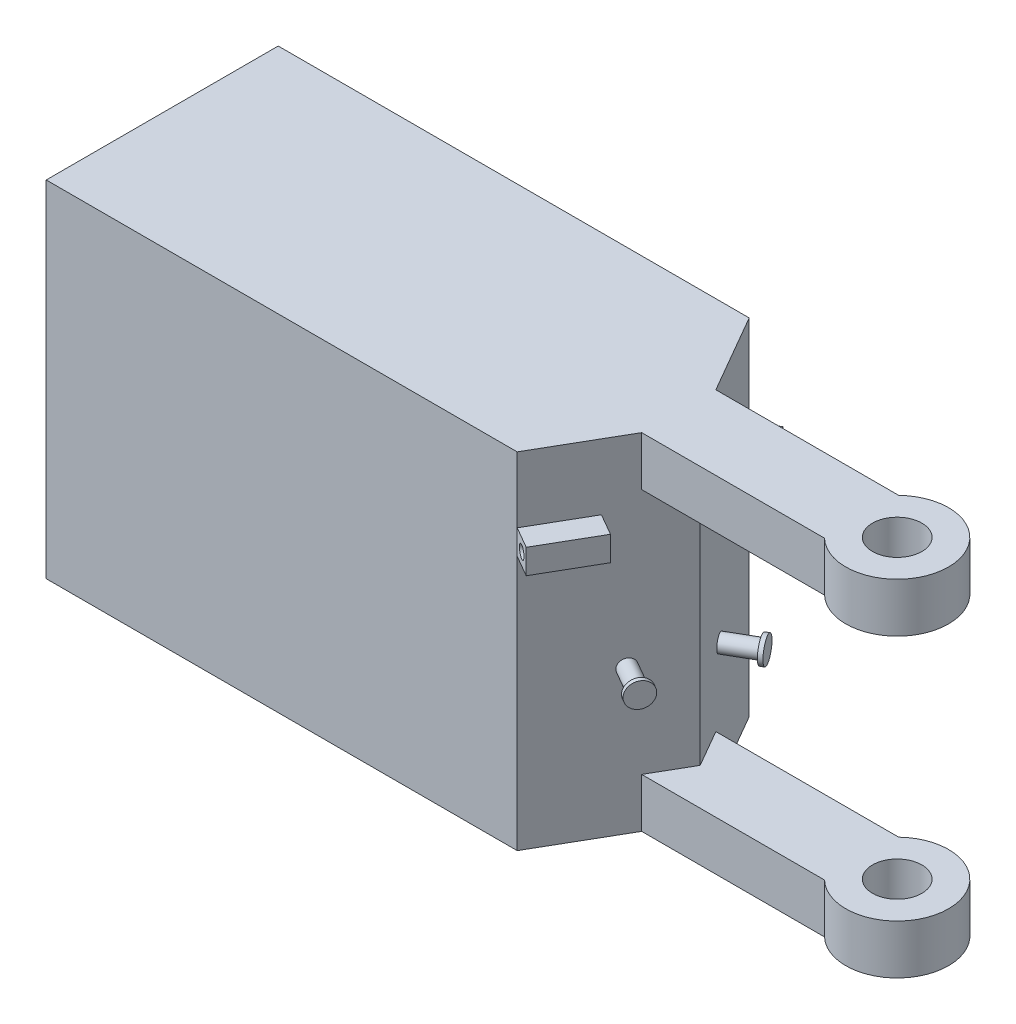
SolidWorks part; units mm, degrees
ref_plane "Front Plane" through (0, 0, 0) normal (0, 0, 1) x (1, 0, 0)
ref_plane "Top Plane" through (0, 0, 0) normal (0, 1, 0) x (1, 0, 0)
ref_plane "Right Plane" through (0, 0, 0) normal (1, 0, 0) x (0, 0, -1)
sketch "Sketch4" plane through (0, 0, 0) normal (0, 1, 0) x (1, 0, 0)
  line L0 (0, 0) -> (220.8953, 0) construction
  line L1 (0, -28.2146) -> (0, 28.2146)
  line L2 (0, 28.2146) -> (114.5561, 28.2146)
  line L3 (114.5561, 28.2146) -> (125.6373, 9.0214)
  line L4 (125.6373, 9.0214) -> (170.1134, 9.0214)
  line L6 (125.6373, -9.0214) -> (170.1134, -9.0214)
  line L7 (114.5561, -28.2146) -> (125.6373, -9.0214)
  line L8 (0, -28.2146) -> (114.5561, -28.2146)
  line L9 (125.6373, 9.0214) -> (130.8458, 0) construction
  circle A0 centre (178.7659, 0) radius 12.5
  circle A2 centre (178.7659, 0) radius 6
  point P9 (176.8194, 0)
  dimension "D3" = 25
  dimension "D4" = 12
  dimension "D1" = 18.0428
  dimension "D2" = 47.9201
  dimension "D5" = 120
  dimension "D6" = 120
extrude "Boss-Extrude2" add sketch "Sketch4" along normal blind 12
sketch "Sketch6" plane through (0, 12, 0) normal (0, 1, 0) x (1, 0, 0)
  line L0 (0, 0) -> (0, 28.2146)
  line L1 (0, -28.2146) -> (0, 28.2146) construction
  line L2 (0, 28.2146) -> (114.5561, 28.2146)
  line L3 (114.5561, 28.2146) -> (125.6373, 9.0214)
  line L4 (125.6373, 9.0214) -> (130.8458, 0)
  line L5 (130.8458, 0) -> (114.5561, -28.2146)
  line L6 (114.5561, -28.2146) -> (0, -28.2146)
  line L7 (0, -28.2146) -> (0, 0)
  line L9 (125.6373, -9.0214) -> (170.1134, -9.0214) construction
  dimension "D1" = 120
extrude "Boss-Extrude3" add sketch "Sketch6" along normal blind 30
mirror "Mirror5" about plane through (0, 42, 0) normal (0, -1, 0) of bodies 103
sketch "Sketch7" plane through (98.1343, 0, 56.6579) normal (0.866, 0, 0.5) x (0.5, 0, -0.866)
  line L6 (52.4079, 42) -> (52.4079, 0) construction
  line L12 (32.8435, 0) -> (55.0059, 0) construction
  line L13 (52.4079, 42) -> (52.4079, 21) construction
sketch "Sketch10" plane through (98.1343, 0, 56.6579) normal (0.866, 0, 0.5) x (0.5, 0, -0.866)
  line L1 (52.4079, 42) -> (52.4079, 0) construction
  line L2 (52.4079, 35) -> (52.4079, 29) construction
sketch "Sketch11" plane through (98.1343, 0, -56.6579) normal (0.866, 0, -0.5) x (-0.5, 0, -0.866)
  line L5 (-52.4079, 21) -> (-52.4079, 29) construction
sketch "Sketch16" plane through (98.1343, 0, -56.6579) normal (0.866, 0, -0.5) x (-0.5, 0, -0.866)
  line L0 (-52.4079, 21) -> (-52.4079, 29) construction
  circle A0 centre (-52.4079, 29) radius 2
extrude "Boss-Extrude9" add sketch "Sketch16" along normal blind 8.5
sketch "Sketch17" plane through (98.1343, 0, 56.6579) normal (0.866, 0, 0.5) x (0.5, 0, -0.866)
  line L0 (52.4079, 0) -> (52.4079, 35) construction
  circle A0 centre (52.4079, 35) radius 2
extrude "Boss-Extrude10" add sketch "Sketch17" along normal blind 8.5
sketch "Sketch9" plane through (98.1343, 0, -56.6579) normal (0.866, 0, -0.5) x (-0.5, 0, -0.866)
sketch "Sketch18" plane through (98.1343, 0, -56.6579) normal (0.866, 0, -0.5) x (-0.5, 0, -0.866)
  line L0 (-32.8435, 84) -> (-32.8435, 59) construction
  line L1 (-32.8435, 84) -> (-32.8435, 0) construction
  line L2 (-32.8435, 59) -> (-32.8435, 56.1904)
  line L3 (-32.8435, 56.1904) -> (-45.94, 56.1904)
  line L4 (-45.94, 56.1904) -> (-45.94, 62.1904)
  line L5 (-45.94, 62.1904) -> (-32.8435, 62.1904)
  line L6 (-32.8435, 62.1904) -> (-32.8435, 59)
  line L7 (-32.8435, 84) -> (-55.0059, 84) construction
  dimension "D1" = 25
extrude "Boss-Extrude11" add sketch "Sketch18" along normal blind 6
sketch "Sketch20" plane through (98.1343, 0, 56.6579) normal (0.866, 0, 0.5) x (0.5, 0, -0.866)
  line L0 (32.8435, 84) -> (32.8435, 0) construction
  line L1 (32.8435, 84) -> (55.0059, 84) construction
  line L3 (32.8435, 68) -> (47.8435, 68)
  line L4 (47.8435, 68) -> (47.8435, 62)
  line L5 (47.8435, 62) -> (32.8435, 62)
  line L7 (32.8435, 68) -> (32.8435, 62)
  dimension "D1" = 16
  dimension "D2" = 22
  dimension "D3" = 15
extrude "Boss-Extrude12" add sketch "Sketch20" along normal blind 6
sketch "Sketch22" plane through (105.4956, 0, -60.9079) normal (0.866, 0, -0.5) x (-0.5, 0, -0.866)
  circle A0 centre (-52.4079, 29) radius 3
extrude "Boss-Extrude13" add sketch "Sketch22" against normal blind 1
sketch "Sketch23" plane through (105.4956, 0, 60.9079) normal (0.866, 0, 0.5) x (0.5, 0, -0.866)
  circle A0 centre (52.4079, 35) radius 3
extrude "Boss-Extrude14" add sketch "Sketch23" against normal blind 1
sketch "Sketch27" plane through (16.4218, 0, 28.4433) normal (-0.5, 0, -0.866) x (-0.866, 0, 0.5)
  line L0 (-113.3158, 59.1904) -> (-117.3158, 59.1904) construction
  line L1 (-113.3158, 56.1904) -> (-113.3158, 62.1904) construction
  circle A0 centre (-117.3158, 59.1904) radius 1.25
extrude "Cut-Extrude4" cut sketch "Sketch27" against normal blind 16
sketch "Sketch28" plane through (23.9218, 0, -41.4337) normal (0.5, 0, -0.866) x (-0.866, 0, -0.5)
  line L0 (-116.3158, 62) -> (-116.3158, 68) construction
  line L1 (-119.3158, 62) -> (-113.3158, 62) construction
  line L2 (-119.3158, 68) -> (-113.3158, 68) construction
  circle A0 centre (-116.3158, 65) radius 1.5
extrude "Cut-Extrude5" cut sketch "Sketch28" against normal blind 17
